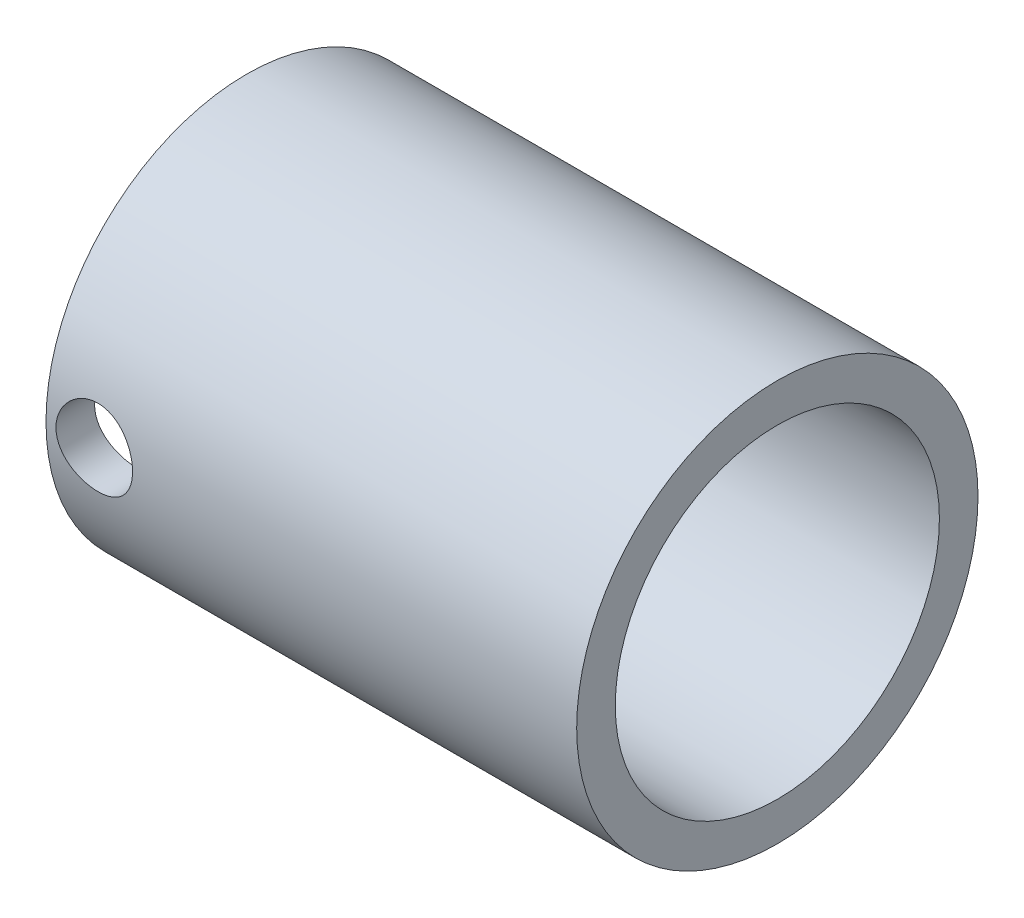
SolidWorks part; units mm, degrees
ref_plane "Front Plane" through (0, 0, 0) normal (0, 0, 1) x (1, 0, 0)
ref_plane "Top Plane" through (0, 0, 0) normal (0, 1, 0) x (1, 0, 0)
ref_plane "Right Plane" through (0, 0, 0) normal (1, 0, 0) x (0, 0, -1)
sketch "Sketch0" plane through (0, 0, 0) normal (0, 0, 1) x (1, 0, 0)
  line L0 (-22, 0) -> (1.5875, 0) construction
  line L2 (-1.5875, 0) -> (1.5875, 0) construction
  line L3 (-22, 0) -> (22, 0) construction
  line L4 (-22, 16.637) -> (-22, -16.637) construction
  line L5 (-1.5875, 13.2842) -> (-22, 13.4366) construction
  line L6 (-1.5875, 13.2842) -> (-1.5875, -13.2842) construction
  line L7 (-1.5875, -13.2842) -> (-22, -13.4366) construction
  line L8 (-22, 13.4366) -> (-22, -13.4366) construction
  line L14 (-1.5875, 10.4648) -> (-1.5875, -10.4648) construction
  dimension "N" = 3.175
  dimension "M" = 33.274
  dimension "OD A" = 26.8732
  dimension "OD B" = 26.5684
  dimension "ID" = 20.9296
  dimension "L" = 44
sketch "Sketch1" plane through (0, 0, 0) normal (0, 0, 1) x (1, 0, 0)
  line L0 (-22, 0) -> (1.5875, 0) construction
  line L1 (-22, 0) -> (1.5875, 0) construction
  line L2 (-1.5875, -10.4648) -> (1.5875, -10.4648)
  line L3 (22, -13.4366) -> (1.5875, -13.2842)
  line L4 (-22, -16.637) -> (-22, -13.4366)
  line L5 (-22, -13.4366) -> (-1.5875, -13.2842)
  line L6 (22, -16.637) -> (22, -13.4366)
  line L7 (-1.5875, -13.2842) -> (-1.5875, -10.4648)
  line L8 (1.5875, -13.2842) -> (1.5875, -10.4648)
  line L9 (22, -16.637) -> (-22, -16.637)
  line L10 (0, 0) -> (0, -10.4648) construction
revolve "Revolve1" add sketch "Sketch1" angle 360 about L1
sketch "Sketch2" plane through (0, 0, 0) normal (0, 0, 1) x (1, 0, 0)
  line L1 (22, -16.637) -> (22, 16.637) construction
  circle A0 centre (-18, 0) radius 3.175
  dimension "D1" = 6.35
  dimension "D2" = 40
extrude "Cut-Extrude1" cut sketch "Sketch2" along normal up to next
